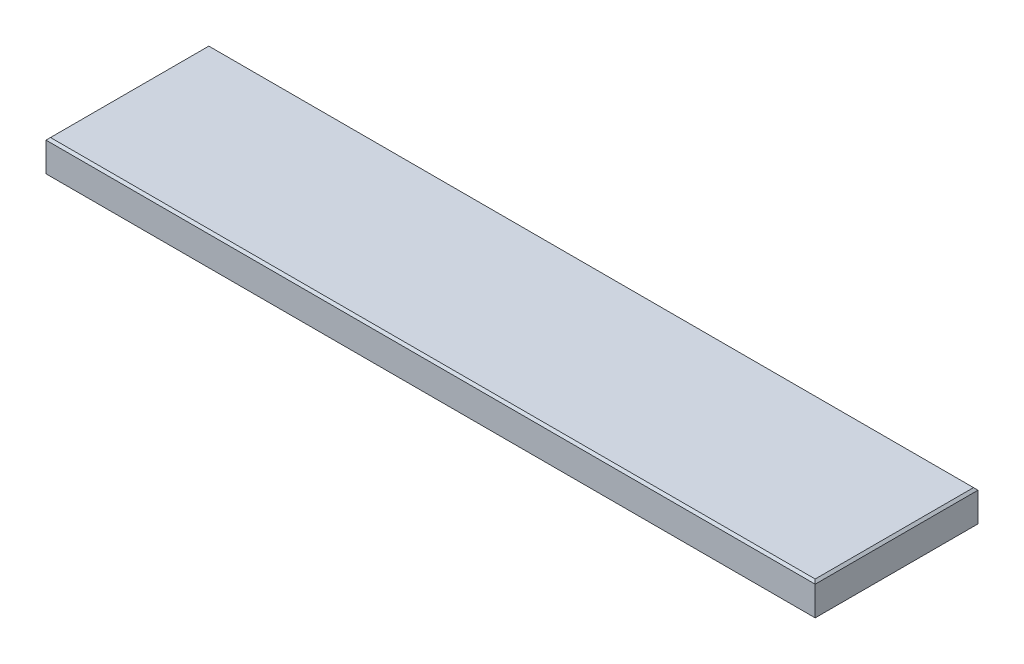
SolidWorks part; units mm, degrees
material "Oak"
ref_plane "Front Plane" through (0, 0, 0) normal (0, 0, 1) x (1, 0, 0)
ref_plane "Top Plane" through (0, 0, 0) normal (0, 1, 0) x (1, 0, 0)
ref_plane "Right Plane" through (0, 0, 0) normal (1, 0, 0) x (0, 0, -1)
sketch "Sketch1" plane through (0, 0, 0) normal (0, 1, 0) x (1, 0, 0)
  line L1 (0, 0) -> (869.95, 0)
  line L2 (0, 0) -> (0, 184.15)
  line L3 (0, 184.15) -> (869.95, 184.15)
  line L4 (869.95, 0) -> (869.95, 184.15)
  dimension "D1" = 184.15
  dimension "D2" = 869.95
extrude "Boss-Extrude1" add sketch "Sketch1" along normal blind 38.1
chamfer "Chamfer1" distance 2.54 angle 45 8 edges at (434.975, 0, 0) (869.95, 0, -92.075) (434.975, 0, -184.15) (0, 0, -92.075) (434.975, 38.1, -184.15) (869.95, 38.1, -92.075) (434.975, 38.1, 0) (0, 38.1, -92.075)
